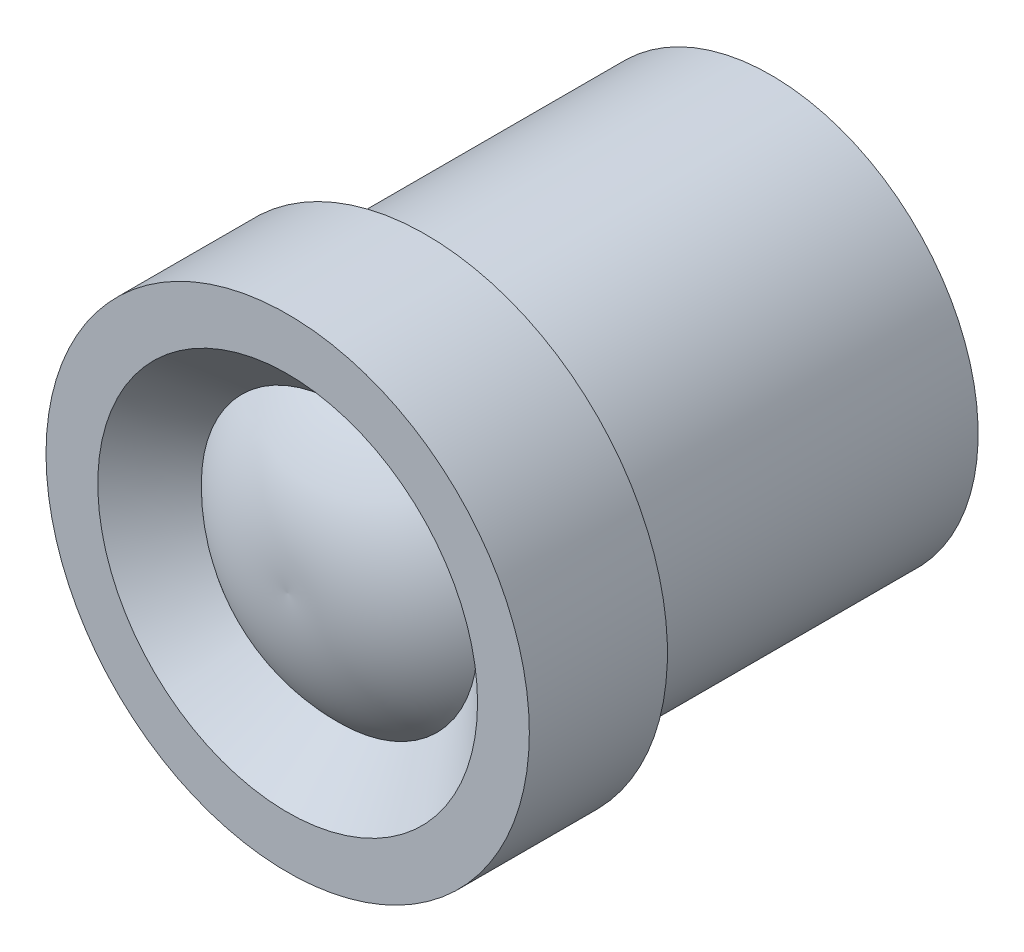
SolidWorks part; units mm, degrees
ref_plane "Front Plane" through (0, 0, 0) normal (0, 0, 1) x (1, 0, 0)
ref_plane "Top Plane" through (0, 0, 0) normal (0, 1, 0) x (1, 0, 0)
ref_plane "Right Plane" through (0, 0, 0) normal (1, 0, 0) x (0, 0, -1)
sketch "Sketch1" plane through (0, 0, 0) normal (0, 0, 1) x (1, 0, 0)
  circle A0 centre (0, 0) radius 7
  dimension "D1" = 14
extrude "Boss-Extrude1" add sketch "Sketch1" along normal blind 14 contours A0
sketch "Sketch2" plane through (0, 0, 0) normal (0, 0, -1) x (-1, 0, 0)
  circle A0 centre (0, 0) radius 6
  dimension "D1" = 12
extrude "Cut-Extrude1" cut sketch "Sketch2" against normal blind 10 flip side to cut
sketch "Sketch3" plane through (0, 0, 14) normal (0, 0, 1) x (1, 0, 0)
  circle A0 centre (0, 0) radius 5.5
  circle A1 centre (0, 0) radius 7 construction
  dimension "D1" = 1.5
extrude "Cut-Extrude2" cut sketch "Sketch3" against normal blind 1.5 draft 45
sketch "Sketch4" plane through (0, 0, 12.5) normal (0, 0, 1) x (1, 0, 0)
  circle A0 centre (0, 0) radius 4
  circle A1 centre (0, 0) radius 4 construction
extrude "Cut-Extrude3" cut sketch "Sketch4" against normal up to surface (12.5 mm away) up to face at (-6, 0, 0)
sketch "Sketch5" plane through (0, 0, 0) normal (0, 0, -1) x (-1, 0, 0)
  circle A0 centre (0, 0) radius 4
  circle A1 centre (0, 0) radius 4 construction
extrude "Boss-Extrude3" add sketch "Sketch5" against normal blind 12.5 separate body
sketch "Sketch6" plane through (0, 0, 0) normal (0, 1, 0) x (1, 0, 0)
  line L0 (-5.5, -14) -> (5.5, -14) construction
  line L1 (-4, -12.5) -> (4, -12.5) construction
  line L2 (4, -12.5) -> (-4, -12.5) construction
  line L3 (4, -12.5) -> (4, 0) construction
  line L4 (-4, -12.5) -> (0, -12.5)
  line L5 (0, -12.5) -> (0, -14)
  arc A0 (-4, -12.5) -> (0, -14) centre (-0.4126, -9.0171) ccw
  point P13 (0, -12.5)
  dimension "D1" = 5
revolve "Revolve1" add sketch "Sketch6" angle 360 about L5
